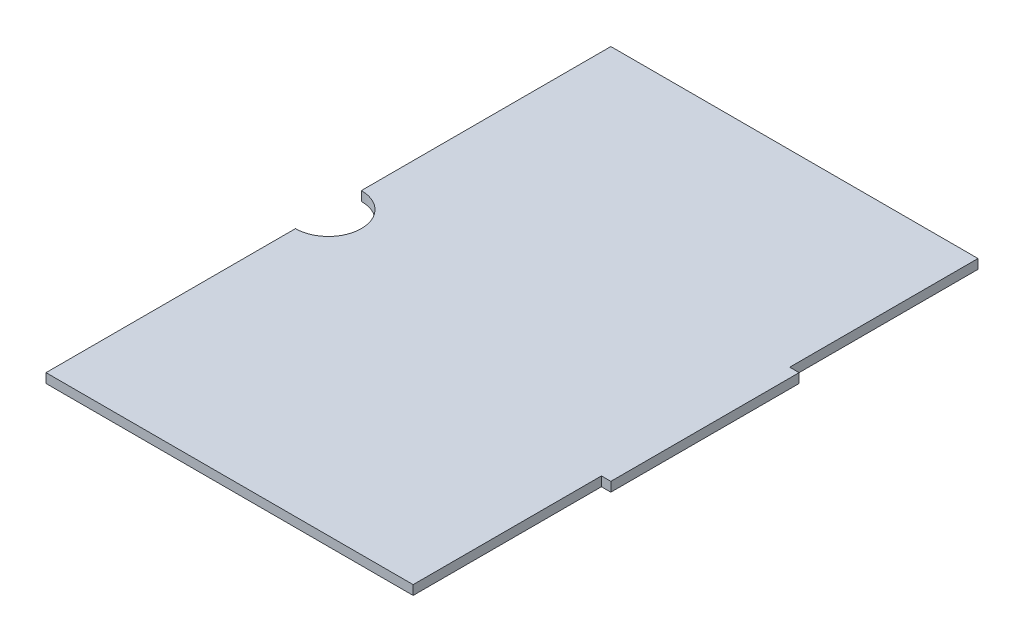
SolidWorks part; units mm, degrees
material "Acrylic (Medium-high impact)"
ref_plane "Front Plane" through (0, 0, 0) normal (0, 0, 1) x (1, 0, 0)
ref_plane "Top Plane" through (0, 0, 0) normal (0, 1, 0) x (1, 0, 0)
ref_plane "Right Plane" through (0, 0, 0) normal (1, 0, 0) x (0, 0, -1)
sketch "Sketch1" plane through (0, 0, 0) normal (0, 1, 0) x (1, 0, 0)
  line L0 (-60, -10.5) -> (-60, -90)
  line L1 (-60, 90) -> (57, 90)
  line L2 (-60, 90) -> (-60, 10.5)
  line L3 (-60, -90) -> (57, -90)
  line L4 (60, 30) -> (60, -30)
  line L5 (57, 30) -> (60, 30)
  line L6 (57, -30) -> (60, -30)
  line L7 (57, 90) -> (57, 30)
  line L8 (57, -30) -> (57, -90)
  arc A0 (-60, -10.5) -> (-60, 10.5) centre (-60, 0) ccw
  point P0 (0, 0)
  dimension "D3" = 21
  dimension "D4" = 60
  dimension "D5" = 60
  dimension "D6" = 3
extrude "Boss-Extrude2" add sketch "Sketch1" along normal blind 3
